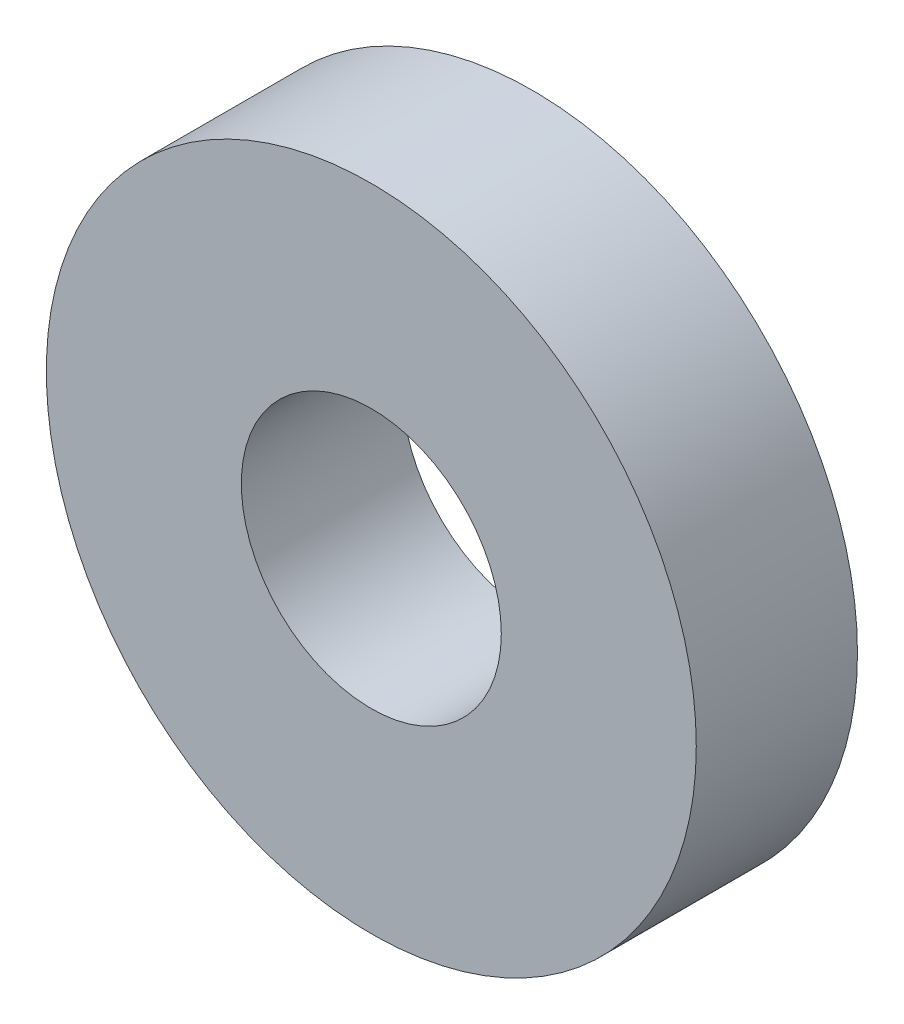
SolidWorks part; units mm, degrees
ref_plane "Front Plane" through (0, 0, 0) normal (0, 0, 1) x (1, 0, 0)
ref_plane "Top Plane" through (0, 0, 0) normal (0, 1, 0) x (1, 0, 0)
ref_plane "Right Plane" through (0, 0, 0) normal (1, 0, 0) x (0, 0, -1)
sketch "Sketch1" plane through (0, 0, 0) normal (0, 0, 1) x (1, 0, 0)
  circle A0 centre (0, 0) radius 6.35
  circle A1 centre (0, 0) radius 15.875
  dimension "D1" = 31.75
  dimension "D2" = 12.7
extrude "Boss-Extrude1" add sketch "Sketch1" along normal mid plane 7.874
